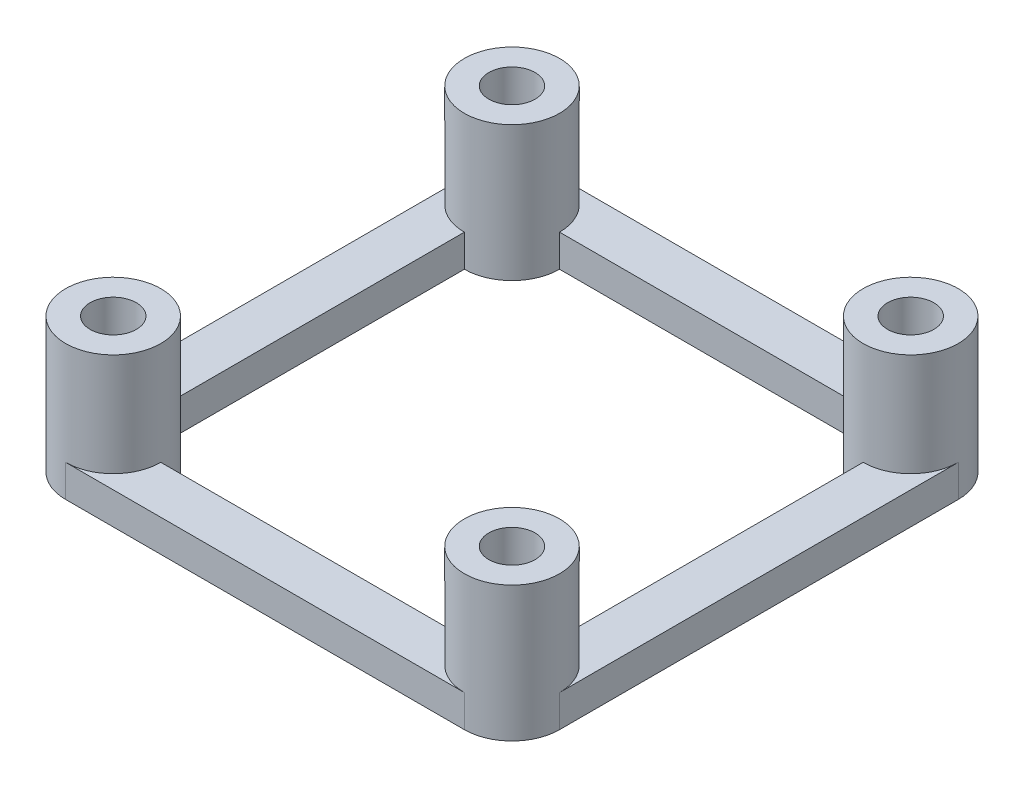
SolidWorks part; units mm, degrees
ref_plane "前视基准面" through (0, 0, 0) normal (0, 0, 1) x (1, 0, 0)
ref_plane "上视基准面" through (0, 0, 0) normal (0, 1, 0) x (1, 0, 0)
ref_plane "右视基准面" through (0, 0, 0) normal (1, 0, 0) x (0, 0, -1)
sketch "草图1" plane through (0, 0, 0) normal (0, 1, 0) x (1, 0, 0)
  line L0 (-19.2, 15.5) -> (-19.2, -15.5)
  line L1 (-15.5, 19.2) -> (15.5, 19.2)
  line L2 (19.2, 15.5) -> (19.2, -15.5)
  line L3 (-15.5, -19.2) -> (15.5, -19.2)
  line L4 (-11.8, 15.5) -> (11.8, 15.5)
  line L5 (15.5, 11.8) -> (15.5, -11.8)
  line L6 (-15.5, 11.8) -> (-15.5, -11.8)
  line L7 (-11.8, -15.5) -> (11.8, -15.5)
  circle A0 centre (-15.5, 15.5) radius 1.8
  circle A1 centre (15.5, 15.5) radius 1.8
  circle A2 centre (-15.5, -15.5) radius 1.8
  circle A3 centre (15.5, -15.5) radius 1.8
  arc A4 (-15.5, 19.2) -> (-19.2, 15.5) centre (-15.5, 15.5) ccw
  arc A5 (19.2, 15.5) -> (15.5, 19.2) centre (15.5, 15.5) ccw
  arc A6 (15.5, -19.2) -> (19.2, -15.5) centre (15.5, -15.5) ccw
  arc A7 (-19.2, -15.5) -> (-15.5, -19.2) centre (-15.5, -15.5) ccw
  arc A8 (-11.8, -15.5) -> (-15.5, -11.8) centre (-15.5, -15.5) ccw
  arc A9 (15.5, -11.8) -> (11.8, -15.5) centre (15.5, -15.5) ccw
  arc A10 (11.8, 15.5) -> (15.5, 11.8) centre (15.5, 15.5) ccw
  arc A11 (-15.5, 11.8) -> (-11.8, 15.5) centre (-15.5, 15.5) ccw
extrude "凸台-拉伸1" add sketch "草图1" along normal blind 2.5
sketch "草图2" plane through (0, 2.5, 0) normal (0, 1, 0) x (1, 0, 0)
  circle A0 centre (-15.5, 15.5) radius 1.8
  circle A1 centre (-15.5, 15.5) radius 3.7
  circle A2 centre (15.5, 15.5) radius 1.8
  circle A3 centre (15.5, 15.5) radius 3.7
  circle A4 centre (15.5, -15.5) radius 1.8
  circle A5 centre (15.5, -15.5) radius 3.7
  circle A6 centre (-15.5, -15.5) radius 1.8
  circle A7 centre (-15.5, -15.5) radius 3.7
extrude "凸台-拉伸2" add sketch "草图2" along normal blind 8
